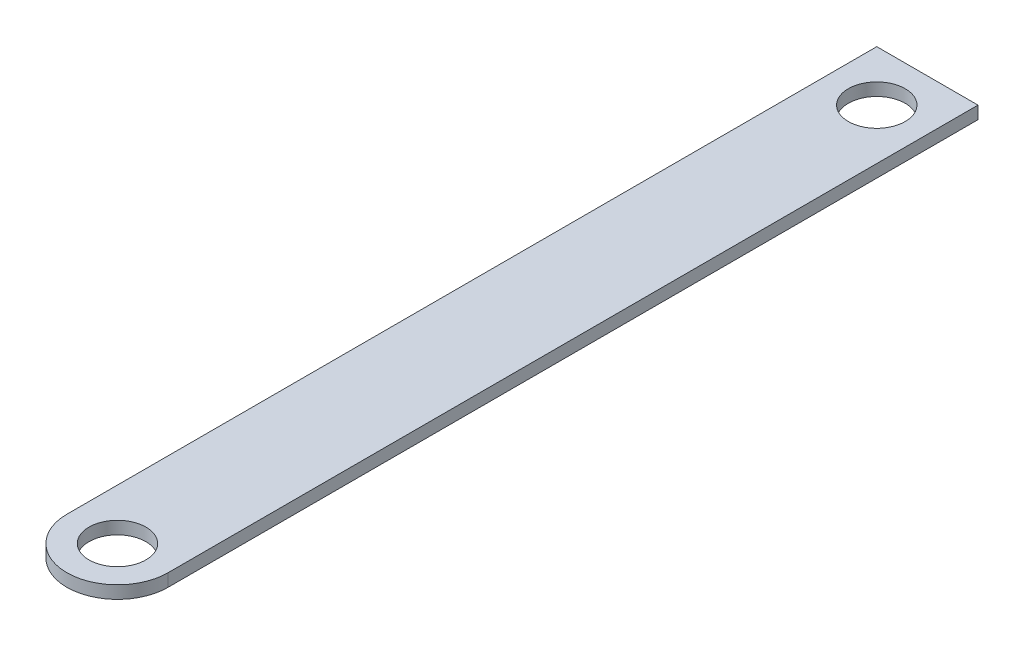
SolidWorks part; units mm, degrees
ref_plane "Front Plane" through (0, 0, 0) normal (0, 0, 1) x (1, 0, 0)
ref_plane "Top Plane" through (0, 0, 0) normal (0, 1, 0) x (1, 0, 0)
ref_plane "Right Plane" through (0, 0, 0) normal (1, 0, 0) x (0, 0, -1)
sketch "Sketch1" plane through (0, 0, 0) normal (0, 1, 0) x (1, 0, 0)
  line L0 (25.4, -25.4) -> (25.4, 0) construction
  line L2 (0, 0) -> (0, 406.4)
  line L3 (0, 406.4) -> (50.8, 406.4)
  line L4 (50.8, 0) -> (50.8, 406.4)
  line L8 (25.4, 406.4) -> (25.4, 381) construction
  arc A0 (0, 0) -> (25.4, -25.4) centre (25.4, 0) ccw
  arc A1 (50.8, 0) -> (25.4, -25.4) centre (25.4, 0) cw
  circle A2 centre (25.4, 0) radius 14.2748
  circle A3 centre (25.4, 381) radius 14.2748
  dimension "D3" = 28.5496
  dimension "D6" = 28.5496
  dimension "D1" = 25.4
  dimension "D2" = 50.8
  dimension "D4" = 431.8
  dimension "D5" = 25.4
extrude "Boss-Extrude1" add sketch "Sketch1" along normal blind 6.35
